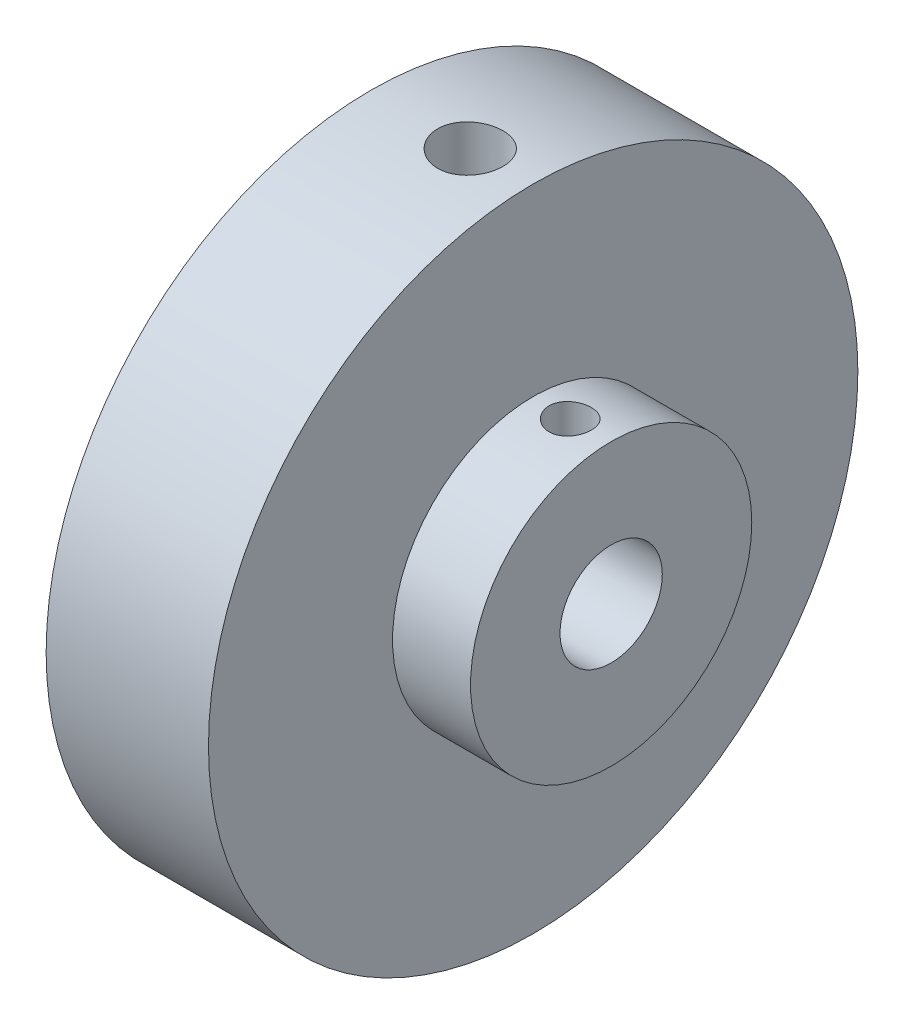
SolidWorks part; units mm, degrees
ref_plane "Front Plane" through (0, 0, 0) normal (0, 0, 1) x (1, 0, 0)
ref_plane "Top Plane" through (0, 0, 0) normal (0, 1, 0) x (1, 0, 0)
ref_plane "Right Plane" through (0, 0, 0) normal (1, 0, 0) x (0, 0, -1)
sketch "Sketch2" plane through (0, 0, 0) normal (1, 0, 0) x (0, 0, -1)
  circle A0 centre (0, 0) radius 11
  dimension "D1" = 22
ref_plane "Plane1" through (0, 25.2, 0) normal (0, 1, 0) x (1, 0, 0)
extrude "Boss-Extrude2" add sketch "Sketch2" along normal blind 6.1
sketch "Sketch7" plane through (6.1, 0, 0) normal (1, 0, 0) x (0, 0, -1)
  circle A0 centre (0, 0) radius 4
  dimension "D1" = 8
extrude "Cut-Extrude3" cut sketch "Sketch7" against normal through all
sketch "Sketch8" plane through (0, 0, 0) normal (-1, 0, 0) x (0, 0, 1)
  circle A0 centre (0, 0) radius 25.4
  dimension "D1" = 50.8
extrude "Boss-Extrude3" add sketch "Sketch8" along normal blind 12.7
sketch "Sketch10" plane through (0, 0, 0) normal (1, 0, 0) x (0, 0, -1)
  circle A0 centre (0, 0) radius 4
  dimension "D1" = 8
extrude "Cut-Extrude5" cut sketch "Sketch10" against normal through all
hole_wizard "1/4-20 Tapped Hole1" positions "3DSketch2" profile "Sketch14" tap size "1/4-20" standard "ANSI Inch" end condition through all
sketch3d "3DSketch2"
  line L0 (0, 0, 0) -> (-4.9212, 0, 0) construction
  line L1 (-4.9212, 0, 0) -> (-4.9212, 33.4074, 0) construction
  line L4 (-4.9212, 33.4074, 0) -> (-4.4793, 33.4074, 0)
  point P3 (-4.9212, 25.4, 0)
  point P46 (-3.752, 25.4, 0)
  point P47 (-6.0904, 25.4, 0)
  point P48 (0, 0, 0)
  point P49 (-4.9212, 25.4, 0)
sketch "Sketch14" plane through (-4.9212, 25.4, 0) normal (1, 0, 0) x (0, 0, 1)
  line L0 (0, 0) -> (0, 50.8)
  line L1 (0, 50.8) -> (2.5527, 50.8)
  line L2 (2.5527, 50.8) -> (2.5527, 0)
  line L5 (2.5527, 0) -> (0, 0)
  line L11 (0, -6.35) -> (0, 107.95) construction
  dimension "Thru Tap Drill Dia." = 5.1054
  dimension "Thru Tap Drill Depth" = 50.8
cosmetic thread "Hole Thread6"
hole_wizard "M4x0.7 Tapped Hole2" positions "3DSketch4" profile "Sketch15" tap size "M4x0.7" standard "ANSI Metric"
sketch3d "3DSketch4"
  point P0 (2.9008, 11, 0)
sketch "Sketch15" plane through (2.9008, 11, 0) normal (1, 0, 0) x (0, 0, 1)
  line L0 (0, 0) -> (0, 12.1674)
  line L1 (0, 12.1674) -> (1.65, 11.176)
  line L2 (1.65, 11.176) -> (1.65, 0)
  line L5 (1.65, 0) -> (0, 0)
  line L10 (0, 12.1674) -> (-1.65, 11.176) construction
  line L11 (0, -6.35) -> (0, 107.95) construction
  dimension "Tap Drill Dia." = 3.3
  dimension "Tap Drill Depth" = 11.176
  dimension "Drill Angle" = 118
cosmetic thread "Hole Thread5"
